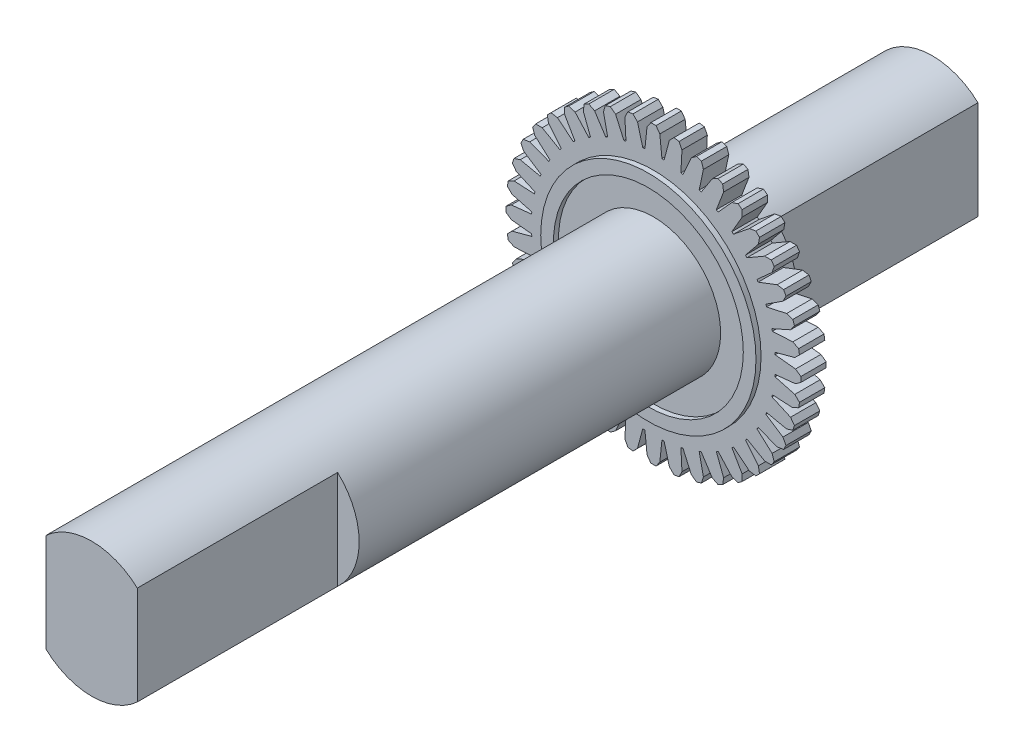
SolidWorks part; units mm, degrees
ref_plane "Front Plane" through (0, 0, 0) normal (0, 0, 1) x (1, 0, 0)
ref_plane "Top Plane" through (0, 0, 0) normal (0, 1, 0) x (1, 0, 0)
ref_plane "Right Plane" through (0, 0, 0) normal (1, 0, 0) x (0, 0, -1)
sketch "Sketch1" plane through (0, 0, 0) normal (0, 0, 1) x (1, 0, 0)
  line L0 (0, 0) -> (0, 5.815) construction
  line L1 (0, 0) -> (0.3359, 4.8033) construction
  line L2 (1.0098, 5.7267) -> (1.1251, 5.4958)
  line L3 (0.1015, 5.8141) -> (0.2515, 5.6041)
  line L4 (0.2515, 5.6041) -> (0.3359, 4.8033)
  line L5 (-0.2515, 5.6041) -> (-0.3359, 4.8033)
  line L6 (-0.1015, 5.8141) -> (-0.2515, 5.6041)
  line L7 (1.1251, 5.4958) -> (1.0831, 4.6916)
  line L8 (0.6283, 5.5745) -> (0.4197, 4.7967)
  line L9 (0.8093, 5.7584) -> (0.6283, 5.5745)
  line L10 (1.8932, 5.4982) -> (1.9709, 5.2521)
  line L11 (1.9709, 5.2521) -> (1.8037, 4.4644)
  line L12 (1.4926, 5.4075) -> (1.1649, 4.672)
  line L13 (1.7001, 5.5609) -> (1.4926, 5.4075)
  line L14 (2.73, 5.1343) -> (2.7683, 4.8791)
  line L15 (2.7683, 4.8791) -> (2.4799, 4.1273)
  line L16 (2.3201, 5.1075) -> (1.8814, 4.4322)
  line L17 (2.5491, 5.2265) -> (2.3201, 5.1075)
  line L18 (3.4996, 4.6441) -> (3.4975, 4.386)
  line L19 (3.4975, 4.386) -> (3.095, 3.6885)
  line L20 (3.0906, 4.6816) -> (2.5516, 4.0834)
  line L21 (3.3353, 4.7634) -> (3.0906, 4.6816)
  line L22 (4.183, 4.0394) -> (4.1405, 3.7849)
  line L23 (4.1405, 3.7849) -> (3.6339, 3.1589)
  line L24 (3.7849, 4.1405) -> (3.1589, 3.6339)
  line L25 (4.0394, 4.183) -> (3.7849, 4.1405)
  line L26 (4.7634, 3.3353) -> (4.6816, 3.0906)
  line L27 (4.6816, 3.0906) -> (4.0834, 2.5516)
  line L28 (4.386, 3.4975) -> (3.6885, 3.095)
  line L29 (4.6441, 3.4996) -> (4.386, 3.4975)
  line L30 (5.2265, 2.5491) -> (5.1075, 2.3201)
  line L31 (5.1075, 2.3201) -> (4.4322, 1.8814)
  line L32 (4.8791, 2.7683) -> (4.1273, 2.4799)
  line L33 (5.1343, 2.73) -> (4.8791, 2.7683)
  line L34 (5.5609, 1.7001) -> (5.4075, 1.4926)
  line L35 (5.4075, 1.4926) -> (4.672, 1.1649)
  line L36 (5.2521, 1.9709) -> (4.4644, 1.8037)
  line L37 (5.4982, 1.8932) -> (5.2521, 1.9709)
  line L38 (5.7584, 0.8093) -> (5.5745, 0.6283)
  line L39 (5.5745, 0.6283) -> (4.7967, 0.4197)
  line L40 (5.4958, 1.1251) -> (4.6916, 1.0831)
  line L41 (5.7267, 1.0098) -> (5.4958, 1.1251)
  line L42 (5.8141, -0.1015) -> (5.6041, -0.2515)
  line L43 (5.6041, -0.2515) -> (4.8033, -0.3359)
  line L44 (5.6041, 0.2515) -> (4.8033, 0.3359)
  line L45 (5.8141, 0.1015) -> (5.6041, 0.2515)
  line L46 (5.7267, -1.0098) -> (5.4958, -1.1251)
  line L47 (5.4958, -1.1251) -> (4.6916, -1.0831)
  line L48 (5.5745, -0.6283) -> (4.7967, -0.4197)
  line L49 (5.7584, -0.8093) -> (5.5745, -0.6283)
  line L50 (5.4982, -1.8932) -> (5.2521, -1.9709)
  line L51 (5.2521, -1.9709) -> (4.4644, -1.8037)
  line L52 (5.4075, -1.4926) -> (4.672, -1.1649)
  line L53 (5.5609, -1.7001) -> (5.4075, -1.4926)
  line L54 (5.1343, -2.73) -> (4.8791, -2.7683)
  line L55 (4.8791, -2.7683) -> (4.1273, -2.4799)
  line L56 (5.1075, -2.3201) -> (4.4322, -1.8814)
  line L57 (5.2265, -2.5491) -> (5.1075, -2.3201)
  line L58 (4.6441, -3.4996) -> (4.386, -3.4975)
  line L59 (4.386, -3.4975) -> (3.6885, -3.095)
  line L60 (4.6816, -3.0906) -> (4.0834, -2.5516)
  line L61 (4.7634, -3.3353) -> (4.6816, -3.0906)
  line L62 (4.0394, -4.183) -> (3.7849, -4.1405)
  line L63 (3.7849, -4.1405) -> (3.1589, -3.6339)
  line L64 (4.1405, -3.7849) -> (3.6339, -3.1589)
  line L65 (4.183, -4.0394) -> (4.1405, -3.7849)
  line L66 (3.3353, -4.7634) -> (3.0906, -4.6816)
  line L67 (3.0906, -4.6816) -> (2.5516, -4.0834)
  line L68 (3.4975, -4.386) -> (3.095, -3.6885)
  line L69 (3.4996, -4.6441) -> (3.4975, -4.386)
  line L70 (2.5491, -5.2265) -> (2.3201, -5.1075)
  line L71 (2.3201, -5.1075) -> (1.8814, -4.4322)
  line L72 (2.7683, -4.8791) -> (2.4799, -4.1273)
  line L73 (2.73, -5.1343) -> (2.7683, -4.8791)
  line L74 (1.7001, -5.5609) -> (1.4926, -5.4075)
  line L75 (1.4926, -5.4075) -> (1.1649, -4.672)
  line L76 (1.9709, -5.2521) -> (1.8037, -4.4644)
  line L77 (1.8932, -5.4982) -> (1.9709, -5.2521)
  line L78 (0.8093, -5.7584) -> (0.6283, -5.5745)
  line L79 (0.6283, -5.5745) -> (0.4197, -4.7967)
  line L80 (1.1251, -5.4958) -> (1.0831, -4.6916)
  line L81 (1.0098, -5.7267) -> (1.1251, -5.4958)
  line L82 (-0.1015, -5.8141) -> (-0.2515, -5.6041)
  line L83 (-0.2515, -5.6041) -> (-0.3359, -4.8033)
  line L84 (0.2515, -5.6041) -> (0.3359, -4.8033)
  line L85 (0.1015, -5.8141) -> (0.2515, -5.6041)
  line L86 (-1.0098, -5.7267) -> (-1.1251, -5.4958)
  line L87 (-1.1251, -5.4958) -> (-1.0831, -4.6916)
  line L88 (-0.6283, -5.5745) -> (-0.4197, -4.7967)
  line L89 (-0.8093, -5.7584) -> (-0.6283, -5.5745)
  line L90 (-1.8932, -5.4982) -> (-1.9709, -5.2521)
  line L91 (-1.9709, -5.2521) -> (-1.8037, -4.4644)
  line L92 (-1.4926, -5.4075) -> (-1.1649, -4.672)
  line L93 (-1.7001, -5.5609) -> (-1.4926, -5.4075)
  line L94 (-2.73, -5.1343) -> (-2.7683, -4.8791)
  line L95 (-2.7683, -4.8791) -> (-2.4799, -4.1273)
  line L96 (-2.3201, -5.1075) -> (-1.8814, -4.4322)
  line L97 (-2.5491, -5.2265) -> (-2.3201, -5.1075)
  line L98 (-3.4996, -4.6441) -> (-3.4975, -4.386)
  line L99 (-3.4975, -4.386) -> (-3.095, -3.6885)
  line L100 (-3.0906, -4.6816) -> (-2.5516, -4.0834)
  line L101 (-3.3353, -4.7634) -> (-3.0906, -4.6816)
  line L102 (-4.183, -4.0394) -> (-4.1405, -3.7849)
  line L103 (-4.1405, -3.7849) -> (-3.6339, -3.1589)
  line L104 (-3.7849, -4.1405) -> (-3.1589, -3.6339)
  line L105 (-4.0394, -4.183) -> (-3.7849, -4.1405)
  line L106 (-4.7634, -3.3353) -> (-4.6816, -3.0906)
  line L107 (-4.6816, -3.0906) -> (-4.0834, -2.5516)
  line L108 (-4.386, -3.4975) -> (-3.6885, -3.095)
  line L109 (-4.6441, -3.4996) -> (-4.386, -3.4975)
  line L110 (-5.2265, -2.5491) -> (-5.1075, -2.3201)
  line L111 (-5.1075, -2.3201) -> (-4.4322, -1.8814)
  line L112 (-4.8791, -2.7683) -> (-4.1273, -2.4799)
  line L113 (-5.1343, -2.73) -> (-4.8791, -2.7683)
  line L114 (-5.5609, -1.7001) -> (-5.4075, -1.4926)
  line L115 (-5.4075, -1.4926) -> (-4.672, -1.1649)
  line L116 (-5.2521, -1.9709) -> (-4.4644, -1.8037)
  line L117 (-5.4982, -1.8932) -> (-5.2521, -1.9709)
  line L118 (-5.7584, -0.8093) -> (-5.5745, -0.6283)
  line L119 (-5.5745, -0.6283) -> (-4.7967, -0.4197)
  line L120 (-5.4958, -1.1251) -> (-4.6916, -1.0831)
  line L121 (-5.7267, -1.0098) -> (-5.4958, -1.1251)
  line L122 (-5.8141, 0.1015) -> (-5.6041, 0.2515)
  line L123 (-5.6041, 0.2515) -> (-4.8033, 0.3359)
  line L124 (-5.6041, -0.2515) -> (-4.8033, -0.3359)
  line L125 (-5.8141, -0.1015) -> (-5.6041, -0.2515)
  line L126 (-5.7267, 1.0098) -> (-5.4958, 1.1251)
  line L127 (-5.4958, 1.1251) -> (-4.6916, 1.0831)
  line L128 (-5.5745, 0.6283) -> (-4.7967, 0.4197)
  line L129 (-5.7584, 0.8093) -> (-5.5745, 0.6283)
  line L130 (-5.4982, 1.8932) -> (-5.2521, 1.9709)
  line L131 (-5.2521, 1.9709) -> (-4.4644, 1.8037)
  line L132 (-5.4075, 1.4926) -> (-4.672, 1.1649)
  line L133 (-5.5609, 1.7001) -> (-5.4075, 1.4926)
  line L134 (-5.1343, 2.73) -> (-4.8791, 2.7683)
  line L135 (-4.8791, 2.7683) -> (-4.1273, 2.4799)
  line L136 (-5.1075, 2.3201) -> (-4.4322, 1.8814)
  line L137 (-5.2265, 2.5491) -> (-5.1075, 2.3201)
  line L138 (-4.6441, 3.4996) -> (-4.386, 3.4975)
  line L139 (-4.386, 3.4975) -> (-3.6885, 3.095)
  line L140 (-4.6816, 3.0906) -> (-4.0834, 2.5516)
  line L141 (-4.7634, 3.3353) -> (-4.6816, 3.0906)
  line L142 (-4.0394, 4.183) -> (-3.7849, 4.1405)
  line L143 (-3.7849, 4.1405) -> (-3.1589, 3.6339)
  line L144 (-4.1405, 3.7849) -> (-3.6339, 3.1589)
  line L145 (-4.183, 4.0394) -> (-4.1405, 3.7849)
  line L146 (-3.3353, 4.7634) -> (-3.0906, 4.6816)
  line L147 (-3.0906, 4.6816) -> (-2.5516, 4.0834)
  line L148 (-3.4975, 4.386) -> (-3.095, 3.6885)
  line L149 (-3.4996, 4.6441) -> (-3.4975, 4.386)
  line L150 (-2.5491, 5.2265) -> (-2.3201, 5.1075)
  line L151 (-2.3201, 5.1075) -> (-1.8814, 4.4322)
  line L152 (-2.7683, 4.8791) -> (-2.4799, 4.1273)
  line L153 (-2.73, 5.1343) -> (-2.7683, 4.8791)
  line L154 (-1.7001, 5.5609) -> (-1.4926, 5.4075)
  line L155 (-1.4926, 5.4075) -> (-1.1649, 4.672)
  line L156 (-1.9709, 5.2521) -> (-1.8037, 4.4644)
  line L157 (-1.8932, 5.4982) -> (-1.9709, 5.2521)
  line L158 (-0.8093, 5.7584) -> (-0.6283, 5.5745)
  line L159 (-0.6283, 5.5745) -> (-0.4197, 4.7967)
  line L160 (-1.1251, 5.4958) -> (-1.0831, 4.6916)
  line L161 (-1.0098, 5.7267) -> (-1.1251, 5.4958)
  arc A0 (0.1015, 5.8141) -> (-0.1015, 5.8141) centre (0, 0) ccw
  arc A1 (-2.4799, 4.1273) -> (-2.5516, 4.0834) centre (0, 0) ccw
  arc A2 (1.0098, 5.7267) -> (0.8093, 5.7584) centre (0, 0) ccw
  circle A3 centre (0, 0) radius 5.815 construction
  arc A4 (1.8932, 5.4982) -> (1.7001, 5.5609) centre (0, 0) ccw
  arc A5 (2.73, 5.1343) -> (2.5491, 5.2265) centre (0, 0) ccw
  arc A6 (3.4996, 4.6441) -> (3.3353, 4.7634) centre (0, 0) ccw
  arc A7 (4.183, 4.0394) -> (4.0394, 4.183) centre (0, 0) ccw
  arc A8 (4.7634, 3.3353) -> (4.6441, 3.4996) centre (0, 0) ccw
  arc A9 (5.2265, 2.5491) -> (5.1343, 2.73) centre (0, 0) ccw
  arc A10 (5.5609, 1.7001) -> (5.4982, 1.8932) centre (0, 0) ccw
  arc A11 (5.7584, 0.8093) -> (5.7267, 1.0098) centre (0, 0) ccw
  arc A12 (5.8141, -0.1015) -> (5.8141, 0.1015) centre (0, 0) ccw
  arc A13 (5.7267, -1.0098) -> (5.7584, -0.8093) centre (0, 0) ccw
  arc A14 (5.4982, -1.8932) -> (5.5609, -1.7001) centre (0, 0) ccw
  arc A15 (5.1343, -2.73) -> (5.2265, -2.5491) centre (0, 0) ccw
  arc A16 (4.6441, -3.4996) -> (4.7634, -3.3353) centre (0, 0) ccw
  arc A17 (4.0394, -4.183) -> (4.183, -4.0394) centre (0, 0) ccw
  arc A18 (3.3353, -4.7634) -> (3.4996, -4.6441) centre (0, 0) ccw
  arc A19 (2.5491, -5.2265) -> (2.73, -5.1343) centre (0, 0) ccw
  arc A20 (1.7001, -5.5609) -> (1.8932, -5.4982) centre (0, 0) ccw
  arc A21 (0.8093, -5.7584) -> (1.0098, -5.7267) centre (0, 0) ccw
  arc A22 (-0.1015, -5.8141) -> (0.1015, -5.8141) centre (0, 0) ccw
  arc A23 (-1.0098, -5.7267) -> (-0.8093, -5.7584) centre (0, 0) ccw
  arc A24 (-1.8932, -5.4982) -> (-1.7001, -5.5609) centre (0, 0) ccw
  arc A25 (-2.73, -5.1343) -> (-2.5491, -5.2265) centre (0, 0) ccw
  arc A26 (-3.4996, -4.6441) -> (-3.3353, -4.7634) centre (0, 0) ccw
  arc A27 (-4.183, -4.0394) -> (-4.0394, -4.183) centre (0, 0) ccw
  arc A28 (-4.7634, -3.3353) -> (-4.6441, -3.4996) centre (0, 0) ccw
  arc A29 (-5.2265, -2.5491) -> (-5.1343, -2.73) centre (0, 0) ccw
  arc A30 (-5.5609, -1.7001) -> (-5.4982, -1.8932) centre (0, 0) ccw
  arc A31 (-5.7584, -0.8093) -> (-5.7267, -1.0098) centre (0, 0) ccw
  arc A32 (-5.8141, 0.1015) -> (-5.8141, -0.1015) centre (0, 0) ccw
  arc A33 (-5.7267, 1.0098) -> (-5.7584, 0.8093) centre (0, 0) ccw
  arc A34 (-5.4982, 1.8932) -> (-5.5609, 1.7001) centre (0, 0) ccw
  arc A35 (-5.1343, 2.73) -> (-5.2265, 2.5491) centre (0, 0) ccw
  arc A36 (-4.6441, 3.4996) -> (-4.7634, 3.3353) centre (0, 0) ccw
  arc A37 (-4.0394, 4.183) -> (-4.183, 4.0394) centre (0, 0) ccw
  arc A38 (-3.3353, 4.7634) -> (-3.4996, 4.6441) centre (0, 0) ccw
  arc A39 (-2.5491, 5.2265) -> (-2.73, 5.1343) centre (0, 0) ccw
  arc A40 (-1.7001, 5.5609) -> (-1.8932, 5.4982) centre (0, 0) ccw
  arc A41 (-0.8093, 5.7584) -> (-1.0098, 5.7267) centre (0, 0) ccw
  arc A42 (-1.8037, 4.4644) -> (-1.8814, 4.4322) centre (0, 0) ccw
  circle A43 centre (0, 0) radius 4.815 construction
  arc A44 (-1.0831, 4.6916) -> (-1.1649, 4.672) centre (0, 0) ccw
  arc A45 (-0.3359, 4.8033) -> (-0.4197, 4.7967) centre (0, 0) ccw
  arc A46 (0.4197, 4.7967) -> (0.3359, 4.8033) centre (0, 0) ccw
  arc A47 (1.1649, 4.672) -> (1.0831, 4.6916) centre (0, 0) ccw
  arc A48 (1.8814, 4.4322) -> (1.8037, 4.4644) centre (0, 0) ccw
  arc A49 (2.5516, 4.0834) -> (2.4799, 4.1273) centre (0, 0) ccw
  arc A50 (3.1589, 3.6339) -> (3.095, 3.6885) centre (0, 0) ccw
  arc A51 (3.6885, 3.095) -> (3.6339, 3.1589) centre (0, 0) ccw
  arc A52 (4.1273, 2.4799) -> (4.0834, 2.5516) centre (0, 0) ccw
  arc A53 (4.4644, 1.8037) -> (4.4322, 1.8814) centre (0, 0) ccw
  arc A54 (4.6916, 1.0831) -> (4.672, 1.1649) centre (0, 0) ccw
  arc A55 (4.8033, 0.3359) -> (4.7967, 0.4197) centre (0, 0) ccw
  arc A56 (4.7967, -0.4197) -> (4.8033, -0.3359) centre (0, 0) ccw
  arc A57 (4.672, -1.1649) -> (4.6916, -1.0831) centre (0, 0) ccw
  arc A58 (4.4322, -1.8814) -> (4.4644, -1.8037) centre (0, 0) ccw
  arc A59 (4.0834, -2.5516) -> (4.1273, -2.4799) centre (0, 0) ccw
  arc A60 (3.6339, -3.1589) -> (3.6885, -3.095) centre (0, 0) ccw
  arc A61 (3.095, -3.6885) -> (3.1589, -3.6339) centre (0, 0) ccw
  arc A62 (2.4799, -4.1273) -> (2.5516, -4.0834) centre (0, 0) ccw
  arc A63 (1.8037, -4.4644) -> (1.8814, -4.4322) centre (0, 0) ccw
  arc A64 (1.0831, -4.6916) -> (1.1649, -4.672) centre (0, 0) ccw
  arc A65 (0.3359, -4.8033) -> (0.4197, -4.7967) centre (0, 0) ccw
  arc A66 (-0.4197, -4.7967) -> (-0.3359, -4.8033) centre (0, 0) ccw
  arc A67 (-1.1649, -4.672) -> (-1.0831, -4.6916) centre (0, 0) ccw
  arc A68 (-1.8814, -4.4322) -> (-1.8037, -4.4644) centre (0, 0) ccw
  arc A69 (-2.5516, -4.0834) -> (-2.4799, -4.1273) centre (0, 0) ccw
  arc A70 (-3.1589, -3.6339) -> (-3.095, -3.6885) centre (0, 0) ccw
  arc A71 (-3.6885, -3.095) -> (-3.6339, -3.1589) centre (0, 0) ccw
  arc A72 (-4.1273, -2.4799) -> (-4.0834, -2.5516) centre (0, 0) ccw
  arc A73 (-4.4644, -1.8037) -> (-4.4322, -1.8814) centre (0, 0) ccw
  arc A74 (-4.6916, -1.0831) -> (-4.672, -1.1649) centre (0, 0) ccw
  arc A75 (-4.8033, -0.3359) -> (-4.7967, -0.4197) centre (0, 0) ccw
  arc A76 (-4.7967, 0.4197) -> (-4.8033, 0.3359) centre (0, 0) ccw
  arc A77 (-4.672, 1.1649) -> (-4.6916, 1.0831) centre (0, 0) ccw
  arc A78 (-4.4322, 1.8814) -> (-4.4644, 1.8037) centre (0, 0) ccw
  arc A79 (-4.0834, 2.5516) -> (-4.1273, 2.4799) centre (0, 0) ccw
  arc A80 (-3.6339, 3.1589) -> (-3.6885, 3.095) centre (0, 0) ccw
  arc A81 (-3.095, 3.6885) -> (-3.1589, 3.6339) centre (0, 0) ccw
  point P5 (5.5609, 1.7001)
  point P9 (4.815, 0)
  point P250 (0, 0)
  dimension "D1" = 11.63
  dimension "D3" = 4
  dimension "D4" = 40
  dimension "D5" = 0.21
  dimension "D6" = 0.8008
  dimension "D2" = 1
extrude "Boss-Extrude1" add sketch "Sketch1" along normal blind 1
sketch "Sketch2" plane through (0, 0, 1) normal (0, 0, 1) x (1, 0, 0)
  circle A0 centre (0, 0) radius 5.815 construction
  circle A1 centre (0, 0) radius 4.245
  circle A2 centre (0, 0) radius 3.745
  dimension "D1" = 1.57
  dimension "D2" = 0.5
extrude "Boss-Extrude2" add sketch "Sketch2" along normal blind 0.2
sketch "Sketch3" plane through (0, 0, 1) normal (0, 0, 1) x (1, 0, 0)
  circle A0 centre (0, 0) radius 2.65
  dimension "D1" = 5.3
extrude "Boss-Extrude3" add sketch "Sketch3" along normal offset from surface (22.1548 mm away) 8.5
sketch "Sketch4" plane through (0, 0, 0) normal (0, 0, -1) x (-1, 0, 0)
  circle A0 centre (0, 0) radius 2.65 construction
  circle A1 centre (0, 0) radius 2.65
extrude "Boss-Extrude4" add sketch "Sketch4" along normal blind 2
sketch "Sketch6" plane through (0, 0, 23.1548) normal (0, 0, 1) x (1, 0, 0)
  line L0 (-1.8, 2.795) -> (-3.446, 0.7139)
  line L2 (1.8, -2.795) -> (1.8, 4.0611)
  line L4 (-1.8, -2.795) -> (-1.8, 2.795)
  line L5 (-3.446, 0.7139) -> (-3.2043, -1.201)
  line L6 (-3.2043, -1.201) -> (-1.8, -2.795)
  line L7 (1.8, 4.0611) -> (3.6333, 1.9801)
  line L8 (3.6333, 1.9801) -> (3.3282, -0.9593)
  line L9 (3.3282, -0.9593) -> (1.8, -2.795)
  line L10 (0, 0) -> (0, -2.65) construction
  circle A0 centre (0, 0) radius 2.65 construction
  point P0 (0, 0)
  dimension "D1" = 3.6
extrude "Cut-Extrude2" cut sketch "Sketch6" against normal blind 17
sketch "Sketch7" plane through (0, 0, -2) normal (0, 0, -1) x (-1, 0, 0)
  line L2 (1.8, -1.9449) -> (1.8, 1.9449)
  line L3 (-1.8, 1.9449) -> (-1.8, -1.9449)
  line L4 (1.8, -1.9449) -> (1.8, 1.9449)
  line L5 (-1.8, 1.9449) -> (-1.8, -1.9449)
  arc A2 (-1.8, -1.9449) -> (1.8, -1.9449) centre (0, 0) ccw
  arc A3 (1.8, 1.9449) -> (-1.8, 1.9449) centre (0, 0) ccw
  arc A4 (-1.8, -1.9449) -> (1.8, -1.9449) centre (0, 0) ccw
  arc A5 (1.8, 1.9449) -> (-1.8, 1.9449) centre (0, 0) ccw
  dimension "D1" = 0
extrude "Boss-Extrude5" add sketch "Sketch7" along normal blind 8
sketch "Sketch8" plane through (0, 0, 6.1548) normal (0, 0, 1) x (1, 0, 0)
  line L0 (-1.8, -1.9449) -> (-1.8, 1.9449) construction
  line L1 (1.8, 1.9449) -> (1.8, -1.9449) construction
  line L2 (-1.8, -1.9449) -> (-1.8, 1.9449)
  line L3 (1.8, 1.9449) -> (1.8, -1.9449)
  arc A0 (-1.8, 1.9449) -> (-1.8, -1.9449) centre (0, 0) ccw construction
  arc A1 (1.8, -1.9449) -> (1.8, 1.9449) centre (0, 0) ccw construction
  arc A2 (-1.8, 1.9449) -> (-1.8, -1.9449) centre (0, 0) ccw
  arc A3 (1.8, -1.9449) -> (1.8, 1.9449) centre (0, 0) ccw
extrude "Boss-Extrude6" add sketch "Sketch8" along normal offset from surface (9.1 mm away) 0.6
